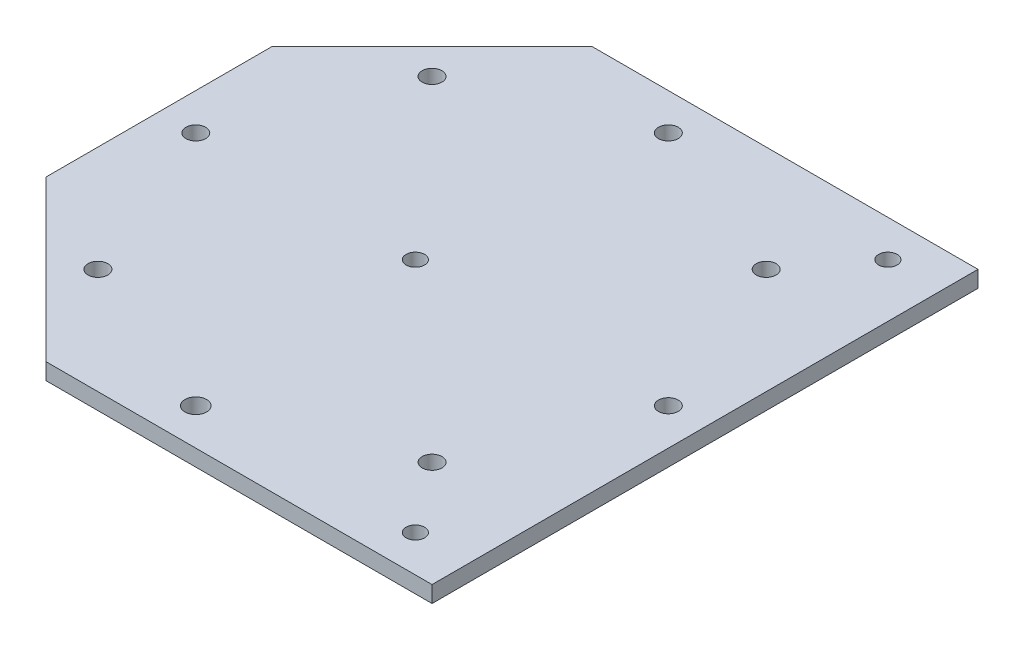
SolidWorks part; units mm, degrees
ref_plane "Front Plane" through (0, 0, 0) normal (0, 0, 1) x (1, 0, 0)
ref_plane "Top Plane" through (0, 0, 0) normal (0, 1, 0) x (1, 0, 0)
ref_plane "Right Plane" through (0, 0, 0) normal (1, 0, 0) x (0, 0, -1)
sketch "Sketch1" plane through (0, 0, 0) normal (0, 1, 0) x (1, 0, 0)
  line L0 (-88.6314, 0) -> (162.72, 0) construction
  line L1 (0, 60.875) -> (0, -60.875) construction
  line L2 (-79.7898, -60.875) -> (81.4786, -60.875) construction
  line L3 (-60.875, 60.875) -> (-60.875, -60.875) construction
  line L4 (-88.6314, 60.875) -> (81.4786, 60.875) construction
  line L5 (60.875, 60.875) -> (60.875, -60.875) construction
  line L6 (-86.0903, 0) -> (0, -86.0903) construction
  line L7 (0, -86.0903) -> (86.0903, 0) construction
  line L8 (86.0903, 0) -> (0, 86.0903) construction
  line L9 (0, 86.0903) -> (-86.0903, 0) construction
  line L10 (-99.4653, 60.875) -> (-99.4653, -41.1995) construction
  line L11 (-19.4653, 60.875) -> (-19.4653, -60.875) construction
  line L12 (0, 0) -> (-60.875, -60.875) construction
  line L13 (80.0047, 60.875) -> (80.0047, -60.875) construction
  line L14 (-88.6314, 0) -> (81.4786, 0) construction
  line L15 (0, 0) -> (-79.537, -32.9453) construction
  line L16 (86.0903, 0) -> (-45.4651, 131.5554) construction
  line L17 (-41.1995, 99.4652) -> (99.4653, 99.4652)
  line L18 (-99.4652, 41.1995) -> (-99.4652, -41.1995)
  line L19 (99.4653, 0) -> (99.4653, 165.2125) construction
  line L20 (-41.1995, 99.4652) -> (-99.4653, 41.1995)
  line L21 (0, 0) -> (-99.4652, 99.4652) construction
  line L22 (-41.1995, -99.4652) -> (99.4653, -99.4652)
  line L23 (99.4653, -99.4652) -> (99.4653, 99.4652)
  line L24 (-27.2873, 113.3775) -> (-113.3775, 27.2873) construction
  line L25 (-41.1995, -99.4652) -> (-99.4652, -41.1995)
  line L26 (-88.6314, -60.875) -> (81.4786, -60.875) construction
  line L27 (-99.4653, 60.875) -> (-99.4653, -60.875) construction
  circle A0 centre (-60.875, -60.875) radius 3.375
  circle A1 centre (60.875, -60.875) radius 3.375
  circle A2 centre (0, 0) radius 86.0903 construction
  circle A3 centre (0, 0) radius 99.4653 construction
  arc A5 (99.4653, 83.8619) -> (99.4653, -83.8619) centre (80.0047, 0) ccw construction
  arc A6 (39.9965, 91.0693) -> (99.4653, -97.5478) centre (80.0047, 0) ccw construction
  circle A8 centre (0, -86.0903) radius 3.9511
  circle A9 centre (-86.0903, 0) radius 3.6069
  circle A10 centre (-60.875, 60.875) radius 3.6069
  circle A11 centre (0, 86.0903) radius 3.6069
  circle A12 centre (60.875, 60.875) radius 3.6069
  circle A13 centre (86.0903, 0) radius 3.6069
  circle A14 centre (60.875, -60.875) radius 3.6069
  circle A15 centre (0, -86.0903) radius 3.6069
  circle A16 centre (-60.875, -60.875) radius 3.6069
  circle A25 centre (80.0048, -86.0902) radius 3.375
  circle A27 centre (-6.0855, 0) radius 3.375
  circle A29 centre (80.0048, 86.0903) radius 3.375
  point P74 (0, 0)
  point P87 (80.0048, 0)
  dimension "D5" = 6.75
  dimension "D6" = 6.75
  dimension "D7" = 121.75
  dimension "D13" = 198.9305
  dimension "D11" = 172.1805
  dimension "D19" = 38.59
  dimension "D10" = 121.75
  dimension "D12" = 80
  dimension "D14" = 99.4653
  dimension "D16" = 99.47
  dimension "D9" = 80.0047
  dimension "D17" = 22.5
  dimension "D1" = 60.875
  dimension "D2" = 60.875
  dimension "D3" = 60.875
  dimension "D4" = 60.875
  dimension "D8" = 13.375
  dimension "D15" = 99.47
  dimension "D18" = 8
extrude "Boss-Extrude1" add sketch "Sketch1" along normal blind 6
